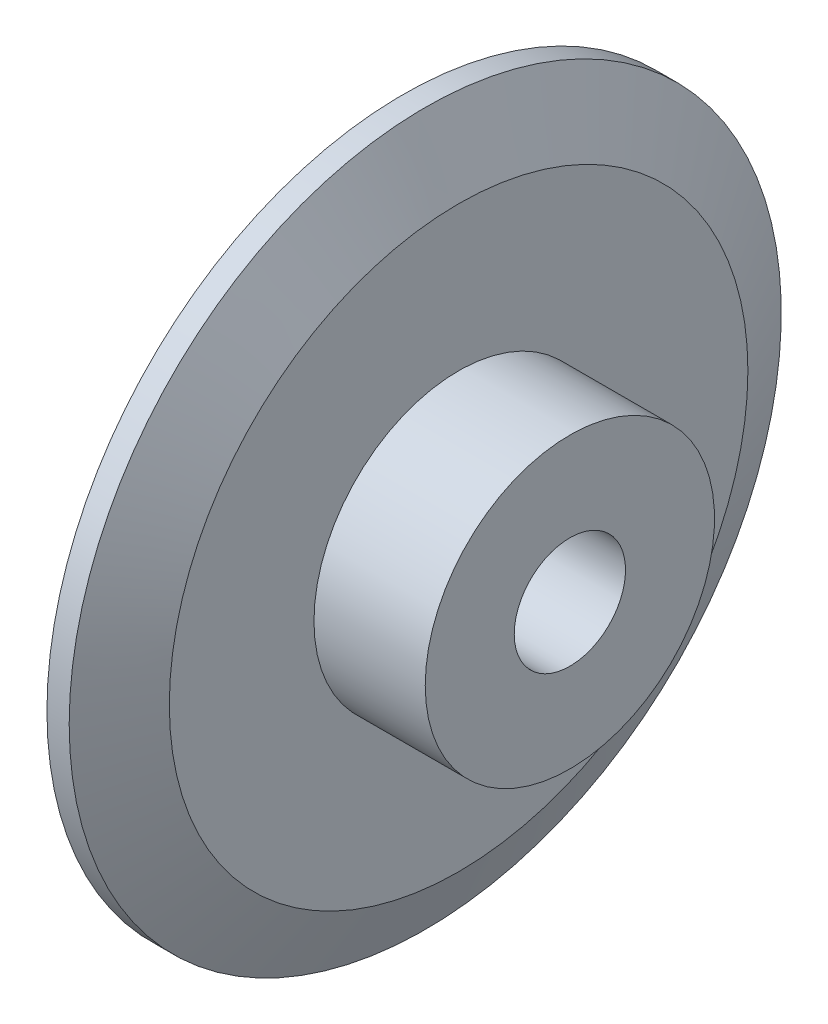
SolidWorks part; units mm, degrees
ref_plane "Plan de face" through (0, 0, 0) normal (0, 0, 1) x (1, 0, 0)
ref_plane "Plan de dessus" through (0, 0, 0) normal (0, 1, 0) x (1, 0, 0)
ref_plane "Plan de droite" through (0, 0, 0) normal (1, 0, 0) x (0, 0, -1)
sketch "Esquisse1" plane through (0, 0, 0) normal (0, 0, 1) x (1, 0, 0)
  line L0 (-14.53, 0) -> (21.3018, 0) construction
  line L1 (-2, 2.5) -> (7, 2.5)
  line L2 (7, 2.5) -> (7, 6.5)
  line L3 (7, 6.5) -> (2, 6.5)
  line L4 (2, 6.5) -> (2, 13)
  line L5 (2, 13) -> (0.5, 16)
  line L6 (0.5, 16) -> (-0.5, 16)
  line L7 (-0.5, 16) -> (-2, 13)
  line L8 (-2, 13) -> (-2, 2.5)
  line L9 (0, 0) -> (0, 37.6755) construction
  dimension "D1" = 5
  dimension "D2" = 32
  dimension "D3" = 4
  dimension "D4" = 4
  dimension "D5" = 1
  dimension "D6" = 3
  dimension "D7" = 5
  dimension "D8" = 9
revolve "Révolution1" add sketch "Esquisse1" angle 360 about L0
